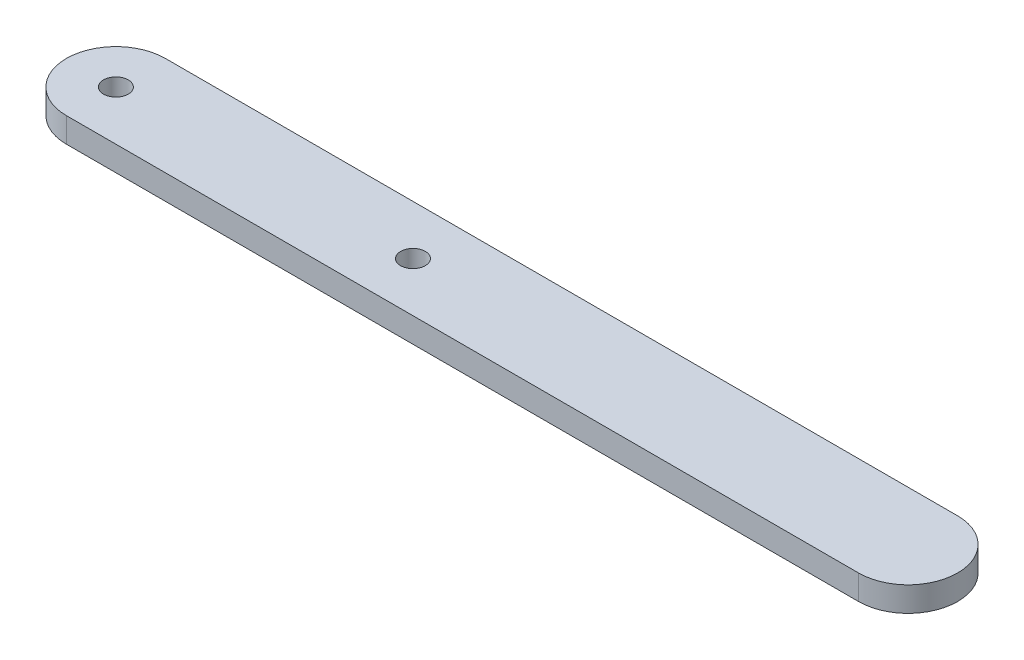
SolidWorks part; units mm, degrees
ref_plane "Front Plane" through (0, 0, 0) normal (0, 0, 1) x (1, 0, 0)
ref_plane "Top Plane" through (0, 0, 0) normal (0, 1, 0) x (1, 0, 0)
ref_plane "Right Plane" through (0, 0, 0) normal (1, 0, 0) x (0, 0, -1)
sketch "Sketch1" plane through (0, 0, 0) normal (0, 1, 0) x (1, 0, 0)
  line L1 (0, 6.35) -> (101.6, 6.35)
  line L3 (0, -6.35) -> (101.6, -6.35)
  arc A0 (0, 6.35) -> (0, -6.35) centre (0, 0) ccw
  arc A1 (101.6, -6.35) -> (101.6, 6.35) centre (101.6, 0) ccw
  circle A3 centre (0, 0) radius 1.5875
  circle A4 centre (38.1, 0) radius 1.5875
  point P8 (38.1, 0)
  dimension "D3" = 3.175
  dimension "D4" = 38.1
  dimension "D1" = 101.6
  dimension "D2" = 12.7
extrude "Boss-Extrude1" add sketch "Sketch1" along normal blind 3.175
